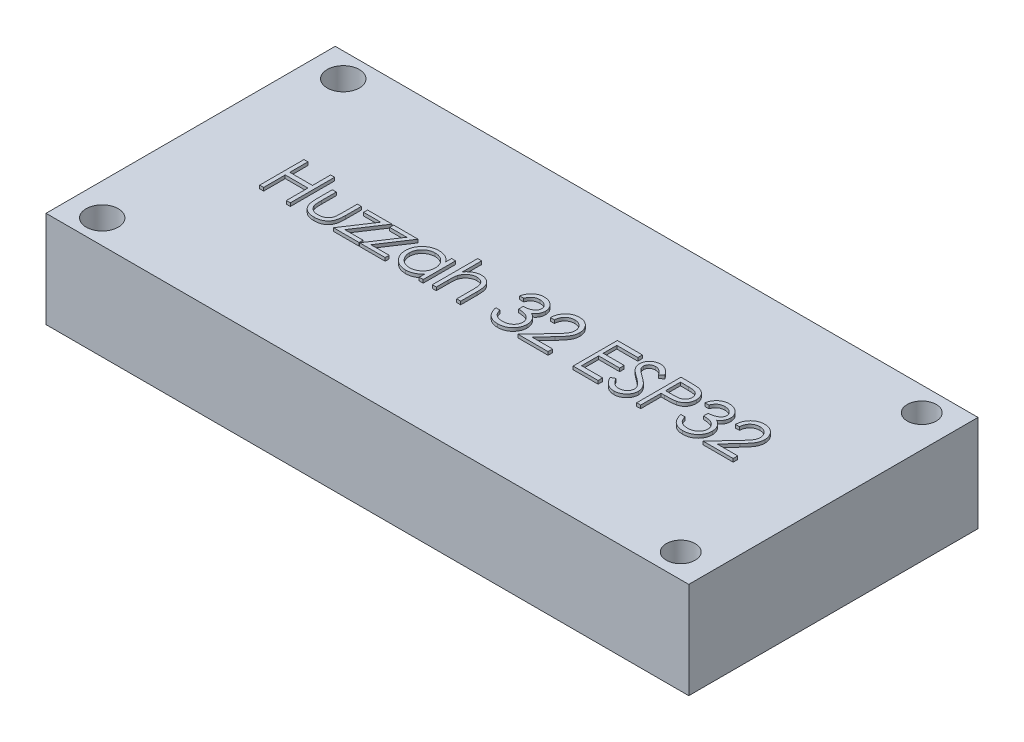
SolidWorks part; units mm, degrees
ref_plane "Front Plane" through (0, 0, 0) normal (0, 0, 1) x (1, 0, 0)
ref_plane "Top Plane" through (0, 0, 0) normal (0, 1, 0) x (1, 0, 0)
ref_plane "Right Plane" through (0, 0, 0) normal (1, 0, 0) x (0, 0, -1)
sketch "Sketch1" plane through (0, 0, 0) normal (0, 1, 0) x (1, 0, 0)
  line L0 (0, 0) -> (-25.4, 0) construction
  line L1 (-25.4, 11.43) -> (25.4, 11.43)
  line L2 (-25.4, 11.43) -> (-25.4, -11.43)
  line L3 (-25.4, -11.43) -> (25.4, -11.43)
  line L4 (25.4, 11.43) -> (25.4, -11.43)
  line L5 (-25.4, 11.43) -> (25.4, -11.43) construction
  line L6 (-25.4, -11.43) -> (25.4, 11.43) construction
  line L7 (-25.4, 0) -> (25.4, 0) construction
  circle A0 centre (-22.86, 9.525) radius 1.27
  circle A1 centre (22.86, 9.525) radius 1.143
  circle A2 centre (22.86, -9.525) radius 1.143
  circle A3 centre (-22.86, -9.525) radius 1.27
  point P0 (0, 0)
  dimension "D3" = 2.54
  dimension "D4" = 2.286
  dimension "D1" = 50.8
  dimension "D2" = 22.86
  dimension "D5" = 1.905
  dimension "D6" = 1.905
  dimension "D7" = 2.54
  dimension "D8" = 2.54
extrude "Boss-Extrude1" add sketch "Sketch1" against normal blind 7.62
sketch "Sketch2" plane through (0, 0, 0) normal (0, 1, 0) x (1, 0, 0)
  text T0 "Huzzah 32 ESP32"
extrude "Boss-Extrude2" add sketch "Sketch2" along normal blind 0.254
